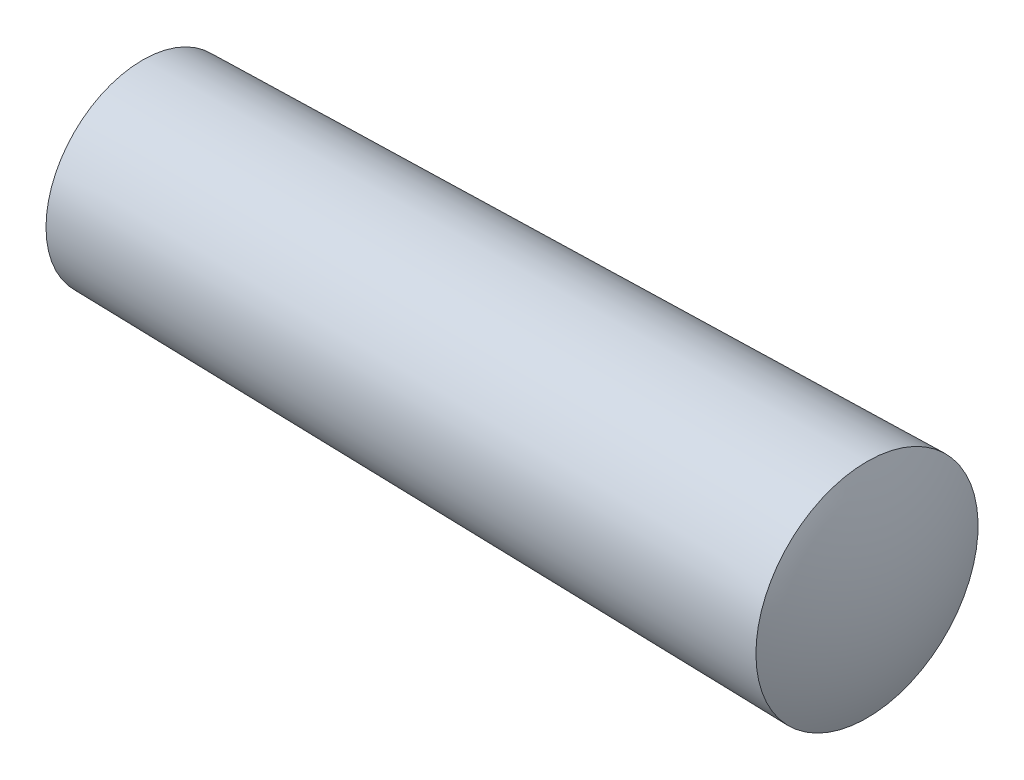
SolidWorks part; units mm, degrees
ref_plane "Front" through (0, 0, 0) normal (0, 0, 1) x (1, 0, 0)
ref_plane "Top" through (0, 0, 0) normal (0, 1, 0) x (1, 0, 0)
ref_plane "Right" through (0, 0, 0) normal (1, 0, 0) x (0, 0, -1)
sketch "Sketch1" plane through (0, 0, 0) normal (0, 0, 1) x (1, 0, 0)
  line L0 (0, 0) -> (32, 0)
  line L1 (1, 4) -> (31, 4) construction
  line L2 (31, 4) -> (31, 4.6) construction
  line L3 (1, 4) -> (31, 4.6)
  line L4 (-4.0035, 0) -> (8.3584, 0) construction
  line L5 (32, 0) -> (32, 2.9125) construction
  line L6 (0, 0) -> (0, -0.8153) construction
  arc A0 (1, 4) -> (0, 0) centre (8.5, 0) ccw
  arc A1 (32, 0) -> (31, 4.6) centre (20.92, 0) ccw
  dimension "l" = 32
  dimension "D5" = 0.6
  dimension "a" = 1
  dimension "d" = 8
  dimension "a1" = 1
revolve "Base-Revolve" add sketch "Sketch1" angle 360 about L4
ref_plane "基准面1" through (4, 0, 0) normal (1, 0, 0) x (0, 0, -1)
equation "\"D5@Sketch1\" = ( \"l@Sketch1\"-2*\"a@Sketch1\")/ 50"
equation "\"a1@Sketch1\" = \"a@Sketch1\""
